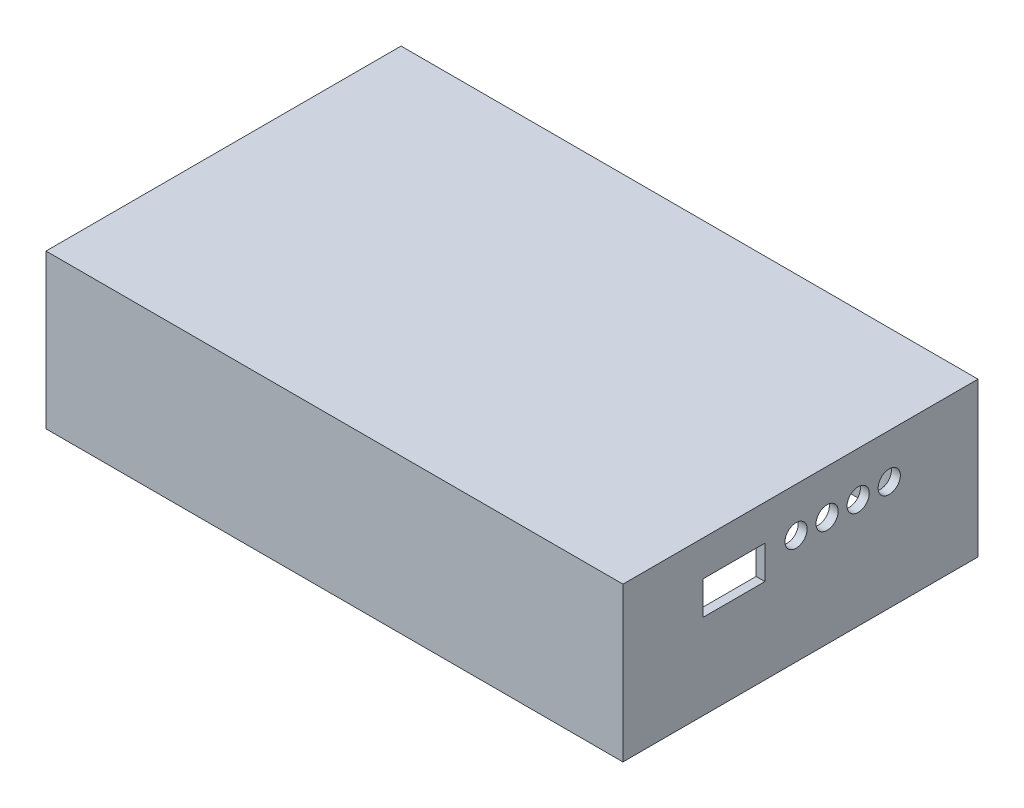
SolidWorks part; units mm, degrees
ref_plane "Plan de face" through (0, 0, 0) normal (0, 0, 1) x (1, 0, 0)
ref_plane "Plan de dessus" through (0, 0, 0) normal (0, 1, 0) x (1, 0, 0)
ref_plane "Plan de droite" through (0, 0, 0) normal (1, 0, 0) x (0, 0, -1)
sketch "Esquisse1" plane through (0, 0, 0) normal (0, 1, 0) x (1, 0, 0)
  line L1 (0, 0) -> (130, 0)
  line L2 (0, 0) -> (0, 80)
  line L3 (0, 80) -> (130, 80)
  line L4 (130, 0) -> (130, 80)
  dimension "D1" = 130
  dimension "D2" = 80
extrude "Boss.-Extru.1" add sketch "Esquisse1" along normal blind 2 contours L3 L4 L1 L2
sketch "Esquisse2" plane through (0, 0, 0) normal (0, -1, 0) x (1, 0, 0)
  line L1 (0, -80) -> (130, -80)
  line L2 (0, -80) -> (0, 0)
  line L3 (0, 0) -> (130, 0)
  line L4 (130, -80) -> (130, 0)
  line L5 (11.899, -78) -> (118.101, -78)
  line L6 (2, -68.101) -> (2, -11.899)
  line L7 (11.899, -2) -> (118.101, -2)
  line L8 (128, -68.101) -> (128, -11.899)
  circle A0 centre (123, -7) radius 5.1
  circle A1 centre (123, -73) radius 5.1
  circle A2 centre (7, -7) radius 5.1
  circle A3 centre (7, -73) radius 5.1
  arc A4 (2, -11.899) -> (11.899, -2) centre (7, -7) ccw
  arc A5 (118.101, -2) -> (128, -11.899) centre (123, -7) ccw
  arc A6 (11.899, -78) -> (2, -68.101) centre (7, -73) ccw
  arc A8 (128, -68.101) -> (118.101, -78) centre (123, -73) ccw
  point P18 (0, 0)
  dimension "D5" = 10.2
  dimension "D6" = 10.2
  dimension "D7" = 10.2
  dimension "D8" = 10.2
  dimension "D9" = 7
  dimension "D10" = 7
  dimension "D11" = 7
  dimension "D12" = 7
  dimension "D13" = 7
  dimension "D14" = 7
  dimension "D15" = 7
  dimension "D16" = 7
  dimension "D17" = 14
  dimension "D18" = 14
  dimension "D19" = 7
  dimension "D20" = 14
  dimension "D1" = 2
  dimension "D2" = 2
  dimension "D3" = 2
  dimension "D4" = 2
extrude "Boss.-Extru.2" add sketch "Esquisse2" along normal blind 32.7
sketch "Esquisse3" plane through (130, 0, 0) normal (1, 0, 0) x (0, 0, -1)
  line L0 (0, 2) -> (0, -32.7) construction
  line L1 (18, -13.5) -> (32, -13.5)
  line L2 (18, -13.5) -> (18, -6)
  line L3 (18, -6) -> (32, -6)
  line L4 (32, -13.5) -> (32, -6)
  line L5 (0, 2) -> (80, 2) construction
  circle A0 centre (39, -8) radius 2.5
  circle A1 centre (46, -8) radius 2.5
  circle A2 centre (53, -8) radius 2.5
  circle A3 centre (60, -8) radius 2.5
  dimension "D5" = 5
  dimension "D6" = 5
  dimension "D7" = 5
  dimension "D8" = 5
  dimension "D10" = 7
  dimension "D11" = 7
  dimension "D12" = 7
  dimension "D13" = 10
  dimension "D14" = 10
  dimension "D15" = 10
  dimension "D16" = 10
  dimension "D1" = 14
  dimension "D2" = 7.5
  dimension "D3" = 18
  dimension "D4" = 8
  dimension "D9" = 7
extrude "Enlèv. mat.-Extru.1" cut sketch "Esquisse3" against normal blind 10
sketch "Esquisse4" plane through (0, 0, 0) normal (0, -1, 0) x (1, 0, 0)
  circle A0 centre (7, -7) radius 5.5
  circle A1 centre (123, -7) radius 5.5
  circle A2 centre (123, -73) radius 5.5
  circle A3 centre (7, -73) radius 5.5
extrude "Boss.-Extru.3" add sketch "Esquisse4" along normal blind 29.5
